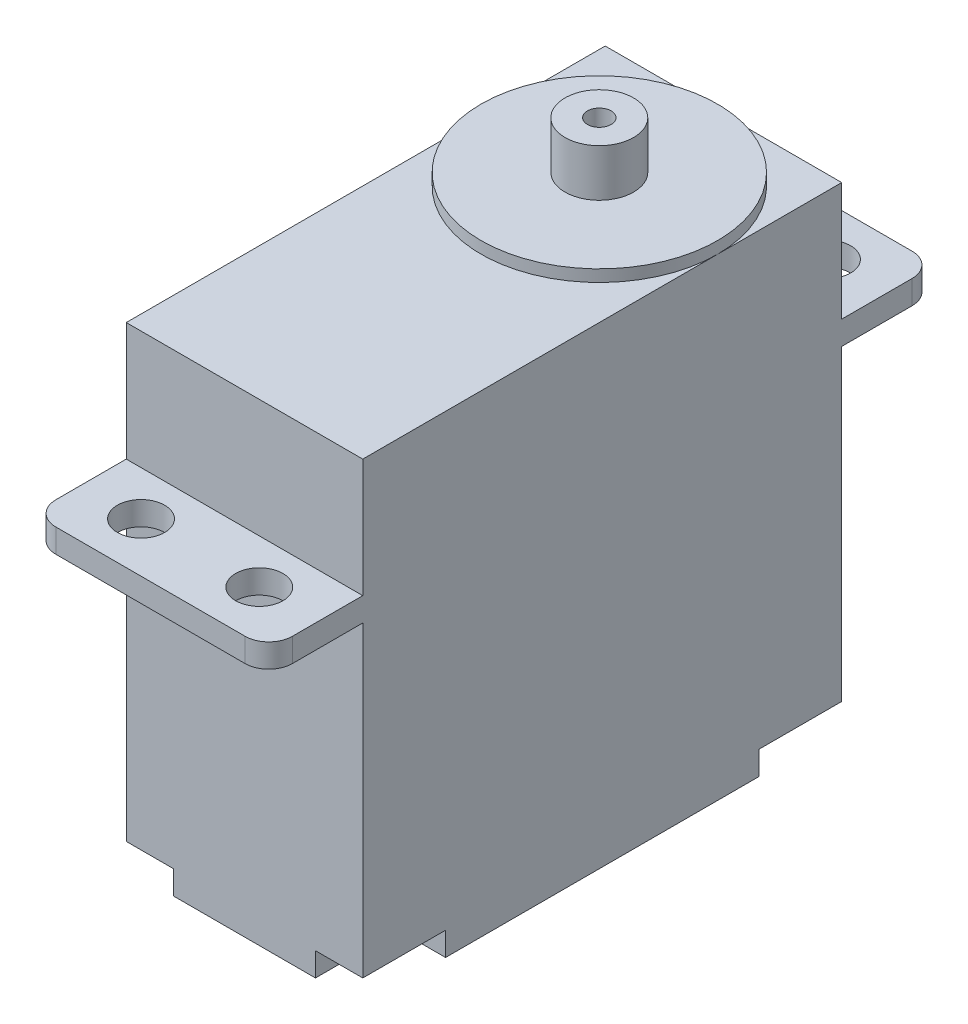
SolidWorks part; units mm, degrees
ref_plane "Front Plane" through (0, 0, 0) normal (0, 0, 1) x (1, 0, 0)
ref_plane "Top Plane" through (0, 0, 0) normal (0, 1, 0) x (1, 0, 0)
ref_plane "Right Plane" through (0, 0, 0) normal (1, 0, 0) x (0, 0, -1)
sketch "Sketch2" plane through (0, 77, 0) normal (0, 1, 0) x (1, 0, 0)
  line L1 (-49.2826, 255.8952) -> (-29.2826, 255.8952)
  line L2 (-49.2826, 255.8952) -> (-49.2826, 296.3952)
  line L3 (-49.2826, 296.3952) -> (-29.2826, 296.3952)
  line L4 (-29.2826, 255.8952) -> (-29.2826, 296.3952)
  dimension "D1" = 40.5
  dimension "D2" = 20
extrude "Boss-Extrude1" add sketch "Sketch2" along normal blind 28
sketch "Sketch3" plane through (0, 105, 0) normal (0, 1, 0) x (1, 0, 0)
  line L0 (-49.2826, 296.3952) -> (-49.2826, 255.8952) construction
  line L1 (-49.2826, 247.9452) -> (-29.2826, 247.9452)
  line L2 (-49.2826, 247.9452) -> (-49.2826, 304.3452)
  line L3 (-49.2826, 304.3452) -> (-29.2826, 304.3452)
  line L4 (-29.2826, 247.9452) -> (-29.2826, 304.3452)
  line L5 (-29.2826, 255.8952) -> (-29.2826, 296.3952) construction
  line L6 (-39.2826, 255.8952) -> (-39.2826, 296.3952) construction
  line L7 (-49.2826, 255.8952) -> (-29.2826, 255.8952) construction
  line L8 (-29.2826, 296.3952) -> (-49.2826, 296.3952) construction
  line L9 (-39.2826, 276.1452) -> (-34.2441, 276.1452) construction
  dimension "D1" = 0
  dimension "D2" = 0
  dimension "D3" = 56.4
  dimension "D4" = 28.2
extrude "Boss-Extrude2" add sketch "Sketch3" along normal blind 2
sketch "Sketch4" plane through (0, 107, 0) normal (0, 1, 0) x (1, 0, 0)
  line L4 (-49.2826, 296.3952) -> (-49.2826, 255.8952)
  line L5 (-29.2826, 296.3952) -> (-49.2826, 296.3952)
  line L6 (-29.2826, 255.8952) -> (-29.2826, 296.3952)
  line L7 (-49.2826, 255.8952) -> (-29.2826, 255.8952)
  line L8 (-49.2826, 296.3952) -> (-49.2826, 255.8952)
  line L9 (-29.2826, 296.3952) -> (-49.2826, 296.3952)
  line L10 (-29.2826, 255.8952) -> (-29.2826, 296.3952)
  line L11 (-49.2826, 255.8952) -> (-29.2826, 255.8952)
  dimension "D1" = 0
extrude "Boss-Extrude3" add sketch "Sketch4" along normal blind 10
sketch "Sketch5" plane through (0, 117, 0) normal (0, 1, 0) x (1, 0, 0)
  line L0 (-29.2826, 255.8952) -> (-29.2826, 296.3952) construction
  line L1 (-49.2826, 296.3952) -> (-49.2826, 255.8952) construction
  line L2 (-49.2826, 255.8952) -> (-29.2826, 255.8952) construction
  circle A0 centre (-39.2826, 285.8952) radius 10
  dimension "D1" = 30
extrude "Boss-Extrude4" add sketch "Sketch5" along normal blind 1
sketch "Sketch6" plane through (0, 118, 0) normal (0, 1, 0) x (1, 0, 0)
  circle A0 centre (-39.2826, 285.8952) radius 2.9
  circle A1 centre (-39.2826, 285.8952) radius 1
extrude "Boss-Extrude5" add sketch "Sketch6" along normal blind 4
sketch "Sketch7" plane through (0, 107, 0) normal (0, 1, 0) x (1, 0, 0)
  circle A0 centre (-44.2826, 252.1452) radius 2
  circle A1 centre (-34.2826, 252.1452) radius 2
  circle A2 centre (-34.2826, 300.1452) radius 2
  circle A3 centre (-44.2826, 300.1452) radius 2
extrude "Cut-Extrude1" cut sketch "Sketch7" against normal blind 2
fillet "Fillet1" radius 2 4 edges at (-29.2826, 106, -304.3452) (-49.2826, 106, -304.3452) (-49.2826, 106, -247.9452) (-29.2826, 106, -247.9452)
sketch "Sketch8" plane through (0, 77, 0) normal (0, -1, 0) x (1, 0, 0)
  line L0 (-39.2826, -255.8952) -> (-39.2826, -296.3952) construction
  line L1 (-29.2826, -255.8952) -> (-33.2826, -255.8952)
  line L2 (-29.2826, -255.8952) -> (-29.2826, -262.8952)
  line L3 (-29.2826, -262.8952) -> (-33.2826, -262.8952)
  line L4 (-33.2826, -255.8952) -> (-33.2826, -262.8952)
  line L5 (-49.2826, -255.8952) -> (-29.2826, -255.8952) construction
  line L6 (-29.2826, -296.3952) -> (-49.2826, -296.3952) construction
  line L7 (-29.2826, -276.1452) -> (-49.2826, -276.1452) construction
  line L8 (-29.2826, -255.8952) -> (-29.2826, -296.3952) construction
  line L9 (-49.2826, -296.3952) -> (-49.2826, -255.8952) construction
  line L10 (-33.2826, -296.3952) -> (-33.2826, -289.3952)
  line L11 (-29.2826, -289.3952) -> (-33.2826, -289.3952)
  line L12 (-29.2826, -296.3952) -> (-29.2826, -289.3952)
  line L13 (-29.2826, -296.3952) -> (-33.2826, -296.3952)
  line L14 (-49.2826, -296.3952) -> (-45.2826, -296.3952)
  line L15 (-49.2826, -296.3952) -> (-49.2826, -289.3952)
  line L16 (-49.2826, -289.3952) -> (-45.2826, -289.3952)
  line L17 (-45.2826, -296.3952) -> (-45.2826, -289.3952)
  line L18 (-45.2826, -255.8952) -> (-45.2826, -262.8952)
  line L19 (-49.2826, -262.8952) -> (-45.2826, -262.8952)
  line L20 (-49.2826, -255.8952) -> (-49.2826, -262.8952)
  line L21 (-49.2826, -255.8952) -> (-45.2826, -255.8952)
extrude "Cut-Extrude2" cut sketch "Sketch8" against normal blind 2
sketch "Sketch9" plane through (0, 0, -296.3952) normal (0, 0, -1) x (-1, 0, 0)
  line L0 (33.2826, 77) -> (45.2826, 77) construction
  line L1 (35.2826, 77) -> (43.2826, 77)
  line L2 (35.2826, 77) -> (35.2826, 80)
  line L3 (35.2826, 80) -> (43.2826, 80)
  line L4 (43.2826, 77) -> (43.2826, 80)
  line L5 (39.2826, 122) -> (39.2826, 77) construction
  line L6 (42.1826, 122) -> (36.3826, 122) construction
  dimension "D1" = 8
  dimension "D2" = 4
  dimension "D3" = 3
extrude "Boss-Extrude6" add sketch "Sketch9" along normal blind 5
ref_plane "Plane1" through (0, 124, 0) normal (0, 1, 0) x (1, 0, 0)
